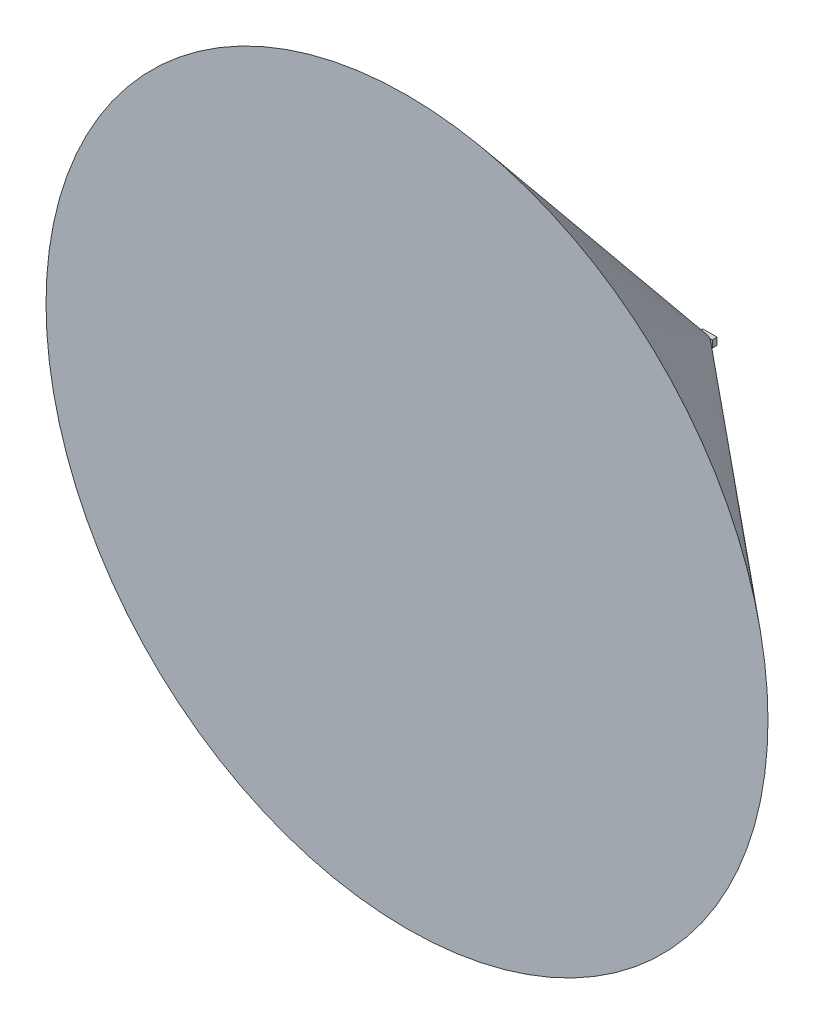
SolidWorks part; units mm, degrees
ref_plane "Front Plane" through (0, 0, 0) normal (0, 0, 1) x (1, 0, 0)
ref_plane "Top Plane" through (0, 0, 0) normal (0, 1, 0) x (1, 0, 0)
ref_plane "Right Plane" through (0, 0, 0) normal (1, 0, 0) x (0, 0, -1)
sketch "Sketch1" plane through (0, 0, 0) normal (0, 0, 1) x (1, 0, 0)
  line L1 (19.05, 9.525) -> (-19.05, 9.525)
  line L2 (19.05, 9.525) -> (19.05, -9.525)
  line L3 (19.05, -9.525) -> (-19.05, -9.525)
  line L4 (-19.05, 9.525) -> (-19.05, -9.525)
  line L5 (19.05, 9.525) -> (-19.05, -9.525) construction
  line L6 (19.05, -9.525) -> (-19.05, 9.525) construction
  point P0 (0, 0)
  dimension "D1" = 19.05
  dimension "D2" = 38.1
extrude "Boss-Extrude1" add sketch "Sketch1" along normal blind 12.7
sketch "Sketch2" plane through (0, 0, 0) normal (1, 0, 0) x (0, 0, -1)
  line L0 (0, 0) -> (-800, 953.4029)
  line L1 (-800, 953.4029) -> (-800, 0)
  line L2 (-800, 0) -> (0, 0)
  dimension "D1" = 800
  dimension "D2" = 50
revolve "Revolve1" add sketch "Sketch2" angle 360 about L2
